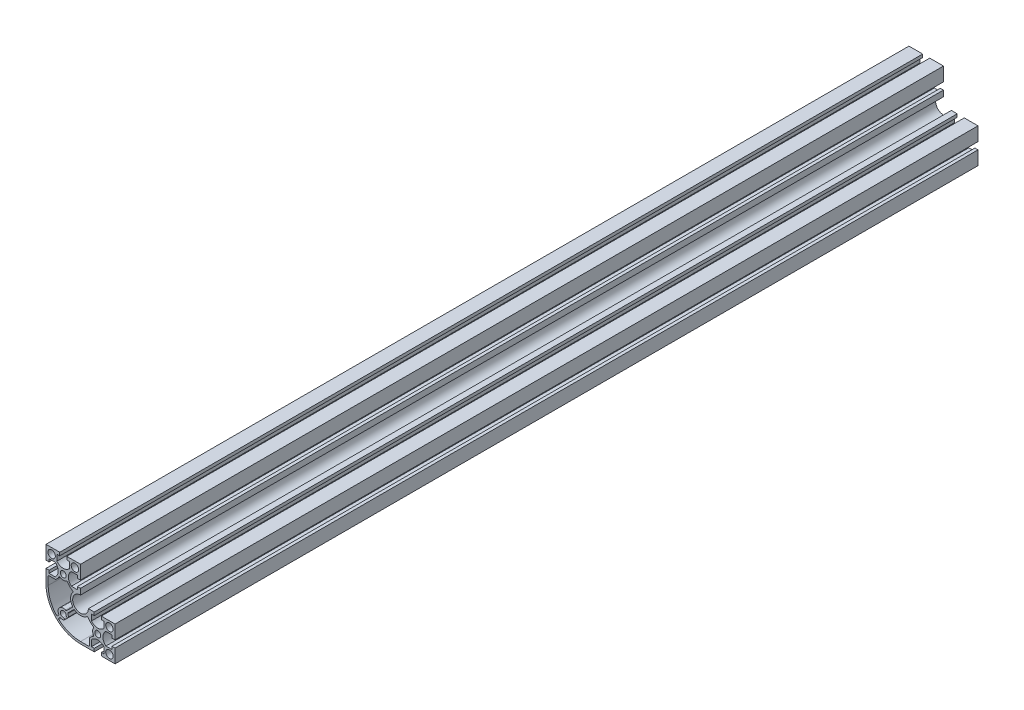
SolidWorks part; units mm, degrees
material "6063 T5"
ref_plane "Спереди" through (0, 0, 0) normal (0, 0, 1) x (1, 0, 0)
ref_plane "Сверху" through (0, 0, 0) normal (0, 1, 0) x (1, 0, 0)
ref_plane "Справа" through (0, 0, 0) normal (1, 0, 0) x (0, 0, -1)
sketch "Эскиз1" plane through (0, 0, 0) normal (0, 0, 1) x (1, 0, 0)
  line L0 (-19.9727, 74.2967) -> (60.0273, 74.2967) construction
  line L1 (0, 40) -> (0, 0) construction
  line L2 (0, 0) -> (40, 0) construction
  line L3 (-20, 47.35) -> (-20, 60)
  line L4 (-20, 60) -> (-7.35, 60)
  line L5 (7.35, 60) -> (20, 60)
  line L6 (20, 60) -> (20, 47.35)
  line L7 (0, 20) -> (-33.7669, 20) construction
  line L8 (-19.989, 66.5236) -> (60.011, 66.5236) construction
  line L9 (-16.5, 30.25) -> (-8.9, 30.25)
  line L10 (-20, 32.65) -> (-20, 20)
  line L11 (0, 0) -> (36.7738, 36.7738) construction
  line L12 (32.65, -20) -> (20, -20)
  line L13 (47.35, -20) -> (60, -20)
  line L14 (60, -20) -> (60, -7.35)
  line L15 (60, 7.35) -> (60, 20)
  line L16 (60, 20) -> (47.35, 20)
  line L17 (20, 32.65) -> (20, 29.1)
  line L18 (29.1, 20) -> (32.65, 20)
  line L39 (10.509, 12.0646) -> (3.9439, 5.4996)
  line L40 (-5.4996, -3.9439) -> (-6.6332, -5.0775)
  line L41 (-17.5, 29.25) -> (-17.5, 20)
  line L42 (29.25, -17.5) -> (20, -17.5)
  line L43 (30.25, -16.5) -> (30.25, -8.9)
  line L44 (12.0646, 10.509) -> (5.4996, 3.9439)
  line L45 (-3.9439, -5.4996) -> (-5.0775, -6.6332)
  circle A0 centre (0, 40) radius 3.4
  circle A1 centre (-13.5, 53.5) radius 4.3
  circle A3 centre (13.5, 53.5) radius 4.3
  arc A5 (3.4, 0) -> (0, -3.4) centre (0, 0) ccw
  circle A6 centre (40, 0) radius 3.4
  circle A7 centre (53.5, 13.5) radius 4.3
  circle A8 centre (53.5, -13.5) radius 4.3
  arc A9 (20, 29.1) -> (29.1, 20) centre (20, 20) ccw
  arc A12 (20, -20) -> (-20, 20) centre (20, 20) cw
  arc A13 (-3.5063, 35.1312) -> (3.4945, 35.1226) centre (0, 40) ccw
  arc A14 (-8.9, 30.25) -> (-4.9633, 34.8081) centre (-18.0527, 42.1339) ccw
  arc A15 (4.9555, 34.7872) -> (10.8502, 28.8371) centre (18.1353, 41.9493) ccw
  arc A16 (11.1354, 27.3259) -> (10.6177, 13.35) centre (20, 20) ccw
  arc A17 (2.7744, 5.32) -> (-5.32, -2.7744) centre (0, 0) ccw
  arc A18 (-17.5, 20) -> (-8.0927, -5.0291) centre (20.5, 20) ccw
  arc A19 (-3.5063, 35.1312) -> (-4.9633, 34.8081) centre (-4.0907, 34.3197) ccw
  arc A20 (3.4945, 35.1226) -> (4.9555, 34.7872) centre (4.0769, 34.3097) cw
  arc A21 (10.8502, 28.8371) -> (11.1354, 27.3259) centre (10.3646, 27.963) cw
  arc A22 (10.6177, 13.35) -> (10.509, 12.0646) centre (9.8019, 12.7717) cw
  arc A23 (3.9439, 5.4996) -> (2.7744, 5.32) centre (3.2368, 6.2067) cw
  arc A24 (-5.32, -2.7744) -> (-5.4996, -3.9439) centre (-6.2067, -3.2368) cw
  arc A25 (-6.6332, -5.0775) -> (-8.0927, -5.0291) centre (-7.3403, -4.3704) cw
  arc A26 (-16.5, 30.25) -> (-17.5, 29.25) centre (-16.5, 29.25) ccw
  arc A27 (30.25, -16.5) -> (29.25, -17.5) centre (29.25, -16.5) cw
  arc A28 (30.25, -8.9) -> (34.8081, -4.9633) centre (42.1339, -18.0527) cw
  arc A29 (35.1312, -3.5063) -> (34.8081, -4.9633) centre (34.3197, -4.0907) cw
  arc A30 (35.1312, -3.5063) -> (35.1226, 3.4945) centre (40, 0) cw
  arc A31 (35.1226, 3.4945) -> (34.7872, 4.9555) centre (34.3097, 4.0769) ccw
  arc A32 (34.7872, 4.9555) -> (28.8371, 10.8502) centre (41.9493, 18.1353) cw
  arc A33 (28.8371, 10.8502) -> (27.3259, 11.1354) centre (27.963, 10.3646) ccw
  arc A34 (27.3259, 11.1354) -> (13.35, 10.6177) centre (20, 20) cw
  arc A35 (13.35, 10.6177) -> (12.0646, 10.509) centre (12.7717, 9.8019) ccw
  arc A36 (5.4996, 3.9439) -> (5.32, 2.7744) centre (6.2067, 3.2368) ccw
  arc A37 (5.32, 2.7744) -> (6, 0) centre (0, 0) cw
  arc A38 (-2.7744, -5.32) -> (-3.9439, -5.4996) centre (-3.2368, -6.2067) ccw
  arc A39 (-5.0775, -6.6332) -> (-5.0291, -8.0927) centre (-4.3704, -7.3403) ccw
  arc A40 (20, -17.5) -> (-5.0291, -8.0927) centre (20, 20.5) cw
  arc A41 (0, -3.4) -> (0, -6) centre (0, -4.7) cw
  arc A42 (3.4, 0) -> (6, 0) centre (4.7, 0) ccw
  arc A43 (0, -6) -> (-2.7744, -5.32) centre (0, 0) cw
  point P7 (-20, 40)
  point P11 (0, 40)
  point P73 (-4.4, 35.9208)
  point P76 (4.4, 35.9208)
  point P79 (12, 28.2614)
  point P90 (-17.5, 30.25)
  line B0 (-20, 47.35) -> (-20, 44.1)
  line B1 (-20, 44.1) -> (-16.4, 44.1)
  line B2 (-16.4, 44.1) -> (-16.4, 47.35)
  line B3 (-16.4, 47.35) -> (-9.4, 47.35)
  line B4 (-9.4, 32.65) -> (-16.4, 32.65)
  line B5 (-16.4, 32.65) -> (-16.4, 35.9)
  line B6 (-16.4, 35.9) -> (-20, 35.9)
  line B7 (-20, 35.9) -> (-20, 32.65)
  line B8 (-20, 47.35) -> (-20, 32.65) construction
  arc B9 (-9.4, 47.35) -> (-9.4, 32.65) centre (-15.4189, 40) cw
  line B10 (7.35, 60) -> (4.1, 60)
  line B11 (4.1, 60) -> (4.1, 56.4)
  line B12 (4.1, 56.4) -> (7.35, 56.4)
  line B13 (7.35, 56.4) -> (7.35, 49.4)
  line B14 (-7.35, 49.4) -> (-7.35, 56.4)
  line B15 (-7.35, 56.4) -> (-4.1, 56.4)
  line B16 (-4.1, 56.4) -> (-4.1, 60)
  line B17 (-4.1, 60) -> (-7.35, 60)
  line B18 (7.35, 60) -> (-7.35, 60) construction
  arc B19 (7.35, 49.4) -> (-7.35, 49.4) centre (0, 55.4189) cw
  line B20 (20, 32.65) -> (20, 35.9)
  line B21 (20, 35.9) -> (16.4, 35.9)
  line B22 (16.4, 35.9) -> (16.4, 32.65)
  line B23 (16.4, 32.65) -> (9.4, 32.65)
  line B24 (9.4, 47.35) -> (16.4, 47.35)
  line B25 (16.4, 47.35) -> (16.4, 44.1)
  line B26 (16.4, 44.1) -> (20, 44.1)
  line B27 (20, 44.1) -> (20, 47.35)
  line B28 (20, 32.65) -> (20, 47.35) construction
  arc B29 (9.4, 32.65) -> (9.4, 47.35) centre (15.4189, 40) cw
  line B30 (32.65, 20) -> (35.9, 20)
  line B31 (35.9, 20) -> (35.9, 16.4)
  line B32 (35.9, 16.4) -> (32.65, 16.4)
  line B33 (32.65, 16.4) -> (32.65, 9.4)
  line B34 (47.35, 9.4) -> (47.35, 16.4)
  line B35 (47.35, 16.4) -> (44.1, 16.4)
  line B36 (44.1, 16.4) -> (44.1, 20)
  line B37 (44.1, 20) -> (47.35, 20)
  line B38 (32.65, 20) -> (47.35, 20) construction
  arc B39 (32.65, 9.4) -> (47.35, 9.4) centre (40, 15.4189) ccw
  line B40 (60, 7.35) -> (60, 4.1)
  line B41 (60, 4.1) -> (56.4, 4.1)
  line B42 (56.4, 4.1) -> (56.4, 7.35)
  line B43 (56.4, 7.35) -> (49.4, 7.35)
  line B44 (49.4, -7.35) -> (56.4, -7.35)
  line B45 (56.4, -7.35) -> (56.4, -4.1)
  line B46 (56.4, -4.1) -> (60, -4.1)
  line B47 (60, -4.1) -> (60, -7.35)
  line B48 (60, 7.35) -> (60, -7.35) construction
  arc B49 (49.4, 7.35) -> (49.4, -7.35) centre (55.4189, 0) ccw
  line B50 (47.35, -20) -> (44.1, -20)
  line B51 (44.1, -20) -> (44.1, -16.4)
  line B52 (44.1, -16.4) -> (47.35, -16.4)
  line B53 (47.35, -16.4) -> (47.35, -9.4)
  line B54 (32.65, -9.4) -> (32.65, -16.4)
  line B55 (32.65, -16.4) -> (35.9, -16.4)
  line B56 (35.9, -16.4) -> (35.9, -20)
  line B57 (35.9, -20) -> (32.65, -20)
  line B58 (47.35, -20) -> (32.65, -20) construction
  arc B59 (47.35, -9.4) -> (32.65, -9.4) centre (40, -15.4189) ccw
  dimension "D3" = 6.8
  dimension "D6" = 8.6
  dimension "D7" = 6.5
  dimension "D10" = 9.1
  dimension "D11" = 40
  dimension "D22" = 1.1
  dimension "D13" = 2.5
  dimension "D15" = 15
  dimension "D16" = 11.5
  dimension "D17" = 6
  dimension "D19" = 4.5
  dimension "D21" = 6
  dimension "D23" = 38
  dimension "D24" = 1
  dimension "D1" = 80
  dimension "D2" = 40
  dimension "D4" = 20
  dimension "D8" = 6.5
  dimension "D12" = 80
  dimension "D14" = 2.4
  dimension "D18" = 8.6
  dimension "D20" = 7.6
  dimension "D5" = 3
sketch_block_instance "8G(14,5С)-1"
sketch_block "8G(14,5С)" parameters "D4"=6.5, "D1"=14.7, "D2"=8.2, "D3"=2.2, "D5"=6
sketch_block_instance "8G(14,5С)-3"
sketch_block_instance "8G(14,5С)-4"
sketch_block_instance "8G(14,5С)-7"
sketch_block_instance "8G(14,5С)-8"
sketch_block_instance "8G(14,5С)-9"
extrude "Бобышка-Вытянуть1" add sketch "Эскиз1" along normal blind 1000 contours B59 B53 B52 B51 B50 L13 L14 B47 B46 B45 B44 B49 B43 B42 B41 B40 L15 L16 B37 B36 B35 B34 B39 B33 B32 B31 B30 L18 A9 L17 B20 B21 B22 B23 B29 B24 B25 B26 B27 L6 L5 B10 B11 B12 B13 B19 B14 B15 B16 B17 L4
